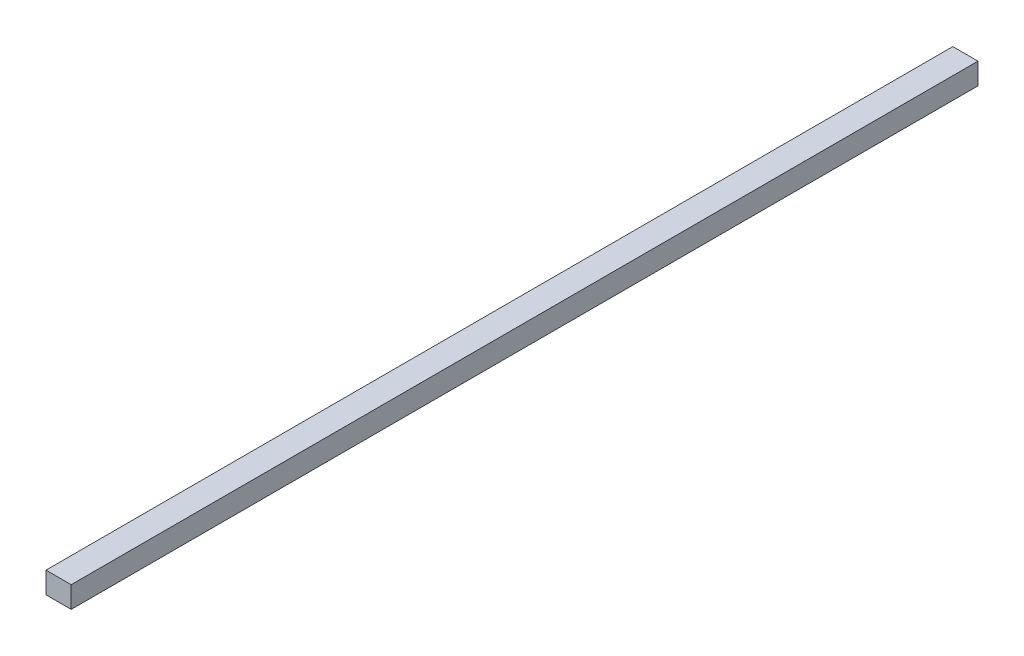
SolidWorks part; units mm, degrees
ref_plane "Front Plane" through (0, 0, 0) normal (0, 0, 1) x (1, 0, 0)
ref_plane "Top Plane" through (0, 0, 0) normal (0, 1, 0) x (1, 0, 0)
ref_plane "Right Plane" through (0, 0, 0) normal (1, 0, 0) x (0, 0, -1)
sketch "Sketch1" plane through (0, 0, 0) normal (1, 0, 0) x (0, 0, -1)
  line L2 (-62.5272, 12.8126) -> (9.4728, 12.8126)
  line L3 (-62.5272, 12.8126) -> (-62.5272, 11.1126)
  line L4 (-62.5272, 11.1126) -> (9.4728, 11.1126)
  line L5 (9.4728, 12.8126) -> (9.4728, 11.1126)
extrude "Boss-Extrude1" add sketch "Sketch1" along normal blind 2
